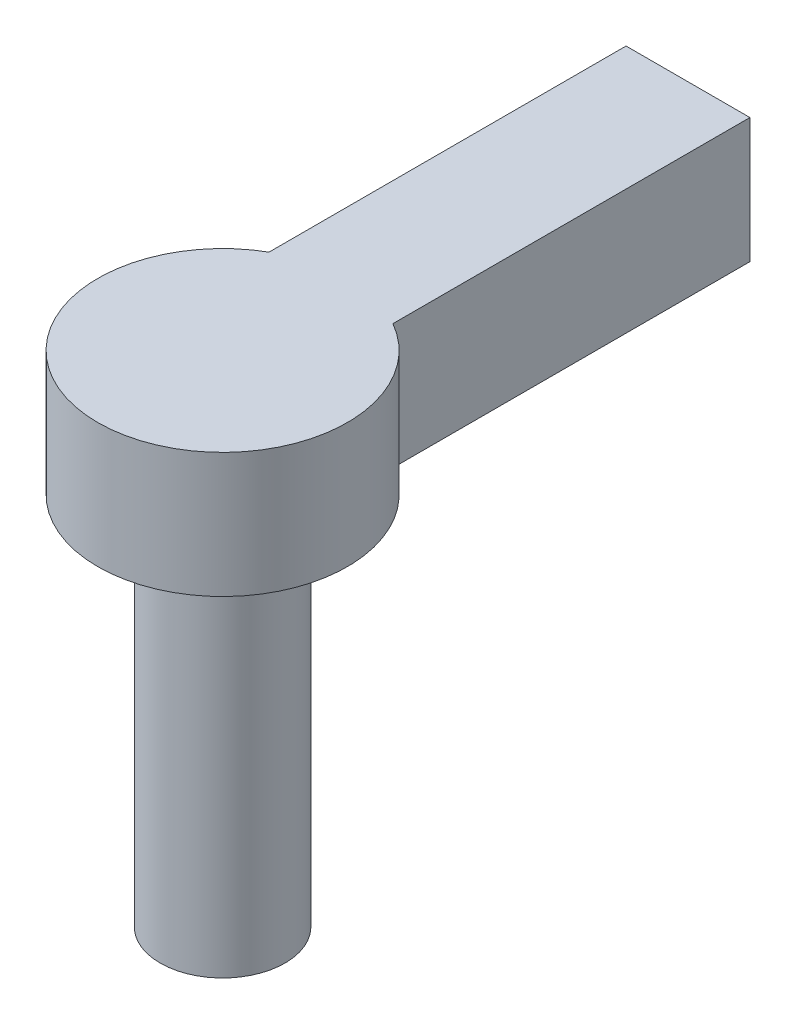
SolidWorks part; units mm, degrees
ref_plane "Front Plane" through (0, 0, 0) normal (0, 0, 1) x (1, 0, 0)
ref_plane "Top Plane" through (0, 0, 0) normal (0, 1, 0) x (1, 0, 0)
ref_plane "Right Plane" through (0, 0, 0) normal (1, 0, 0) x (0, 0, -1)
sketch "Sketch1" plane through (0, 0, 0) normal (0, 1, 0) x (1, 0, 0)
  circle A0 centre (0, 0) radius 3.175
extrude "Boss-Extrude1" add sketch "Sketch1" along normal blind 19.05
sketch "Sketch3" plane through (0, 19.05, 0) normal (0, 1, 0) x (1, 0, 0)
  line L3 (3.1503, 5.5135) -> (3.1503, 8.686)
  line L4 (3.1503, 8.686) -> (-3.1503, 8.686)
  line L5 (-3.1503, 5.5135) -> (-3.1503, 8.686)
  arc A0 (-3.1503, 5.5135) -> (3.1503, 5.5135) centre (0, 0) ccw
  point P4 (0, 6.35)
extrude "Boss-Extrude2" add sketch "Sketch3" along normal blind 6.35
sketch "Sketch4" plane through (0, 0, -8.686) normal (0, 0, -1) x (-1, 0, 0)
  line L4 (-3.1503, 19.05) -> (3.1503, 19.05)
  line L5 (3.1503, 19.05) -> (3.1503, 25.4)
  line L6 (3.1503, 25.4) -> (-3.1503, 25.4)
  line L7 (-3.1503, 25.4) -> (-3.1503, 19.05)
  line L8 (-3.1503, 19.05) -> (3.1503, 19.05)
  line L9 (3.1503, 19.05) -> (3.1503, 25.4)
  line L10 (3.1503, 25.4) -> (-3.1503, 25.4)
  line L11 (-3.1503, 25.4) -> (-3.1503, 19.05)
  dimension "D1" = 0
extrude "Boss-Extrude3" add sketch "Sketch4" along normal blind 14.986
